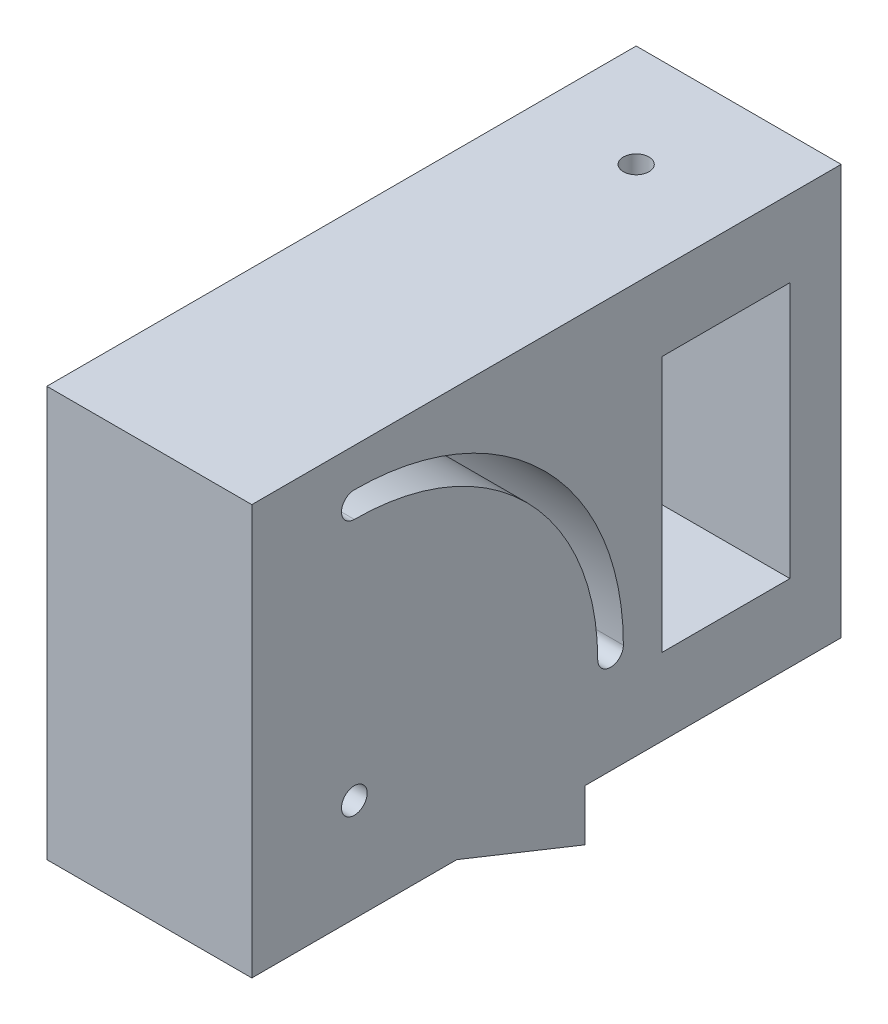
SolidWorks part; units mm, degrees
ref_plane "Alzado" through (0, 0, 0) normal (0, 0, 1) x (1, 0, 0)
ref_plane "Planta" through (0, 0, 0) normal (0, 1, 0) x (1, 0, 0)
ref_plane "Vista lateral" through (0, 0, 0) normal (1, 0, 0) x (0, 0, -1)
ref_plane "Plano1" through (-40, 0, 0) normal (-1, 0, 0) x (0, -1, 0)
sketch "Croquis1" plane through (-40, 0, 0) normal (-1, 0, 0) x (0, -1, 0)
  line L0 (-37.9404, 40) -> (-37.9404, -25)
  line L1 (-37.9404, -25) -> (52.0596, -25)
  line L2 (52.0596, -25) -> (42.0596, 0)
  line L3 (42.0596, 0) -> (42.0596, 40)
  line L4 (42.0596, 40) -> (-37.9404, 40)
extrude "Saliente-Extruir1" add sketch "Croquis1" against normal blind 40
sketch "Croquis2" plane through (0, 0, -25) normal (0, 0, -1) x (-1, 0, 0)
  line L0 (0, -42.0596) -> (0, 37.9404)
  line L1 (0, 37.9404) -> (40, 37.9404)
  line L2 (40, 37.9404) -> (40, -42.0596)
  line L3 (40, -42.0596) -> (0, -42.0596)
extrude "Saliente-Extruir2" add sketch "Croquis2" along normal blind 50
sketch "Croquis3" plane through (-40, 0, 0) normal (-1, 0, 0) x (0, 0, 1)
  arc A0 (-32.5, -22.0596) -> (-27.5, -22.0596) centre (-30, -22.0596) ccw
  arc A1 (-27.5, -22.0596) -> (20, 25.4404) centre (20, -22.0596) cw
  arc A2 (20, 25.4404) -> (20, 30.4404) centre (20, 27.9404) ccw
  arc A3 (20, 30.4404) -> (-32.5, -22.0596) centre (20, -22.0596) ccw
extrude "Cortar-Extruir1" cut sketch "Croquis3" against normal through all
sketch "Croquis4" plane through (0, 0, 0) normal (1, 0, 0) x (0, 0, -1)
  line L0 (65, -27.0596) -> (65, 22.9404)
  line L1 (65, 22.9404) -> (40, 22.9404)
  line L2 (40, 22.9404) -> (40, -27.0596)
  line L3 (40, -27.0596) -> (65, -27.0596)
  dimension "D1" = 25
  dimension "D2" = 50
extrude "Cortar-Extruir2" cut sketch "Croquis4" against normal through all
hole_wizard "Diámetro de taladro Ø5.0 (5)1" positions "Croquis6" profile "Croquis5" hole size "Ø5.0" standard "Ansi Metric"
sketch "Croquis6" plane through (0, -27.0596, 0) normal (0, 1, 0) x (1, 0, 0)
  point P0 (-20, 55)
sketch "Croquis5" plane through (-20, -27.0596, -55) normal (1, 0, 0) x (0, 0, 1)
  line L0 (0, 0) -> (0, 25)
  line L1 (0, 25) -> (2.5, 25)
  line L2 (2.5, 25) -> (2.5, 0)
  line L5 (2.5, 0) -> (0, 0)
  line L11 (0, -6.35) -> (0, 107.95) construction
  dimension "Diámetro de taladro hasta el siguiente" = 5
  dimension "Profundidad de taladro hasta el siguiente" = 25
hole_wizard "Diámetro de taladro Ø5.0 (5)2" positions "Croquis8" profile "Croquis7" hole size "Ø5.0" standard "Ansi Metric"
sketch "Croquis8" plane through (0, 0, 0) normal (1, 0, 0) x (0, 0, -1)
  point P0 (-20, -22.0596)
sketch "Croquis7" plane through (0, -22.0596, 20) normal (0, 1, 0) x (0, 0, -1)
  line L0 (0, 0) -> (0, 40.0001)
  line L1 (0, 40.0001) -> (2.5, 40.0001)
  line L2 (2.5, 40.0001) -> (2.5, 0)
  line L5 (2.5, 0) -> (0, 0)
  line L11 (0, -6.35) -> (0, 107.95) construction
  dimension "Diámetro de taladro hasta el siguiente" = 5
  dimension "Profundidad de taladro hasta el siguiente" = 40.0001
hole_wizard "Diámetro de taladro Ø5.0 (5)3" positions "Croquis10" profile "Croquis9" hole size "Ø5.0" standard "Ansi Metric"
sketch "Croquis10" plane through (0, 37.9404, 0) normal (0, 1, 0) x (1, 0, 0)
  point P0 (-20, 55)
sketch "Croquis9" plane through (-20, 37.9404, -55) normal (1, 0, 0) x (0, 0, 1)
  line L0 (0, 0) -> (0, 90)
  line L1 (0, 90) -> (2.5, 90)
  line L2 (2.5, 90) -> (2.5, 0)
  line L5 (2.5, 0) -> (0, 0)
  line L11 (0, -6.35) -> (0, 107.95) construction
  dimension "Diámetro de taladro hasta el siguiente" = 5
  dimension "Profundidad de taladro hasta el siguiente" = 90
sketch "Croquis12" plane through (0, 0, 0) normal (1, 0, 0) x (0, 0, -1)
  line L0 (65, 22.9404) -> (75, 22.9404)
  line L1 (75, 37.9404) -> (75, -42.0596) construction
  dimension "D1" = 10
sketch "Croquis13" plane through (0, 37.9404, 0) normal (0, 1, 0) x (1, 0, 0)
  line L0 (-20, 75) -> (-20, 55)
  line L1 (-40, 75) -> (0, 75) construction
